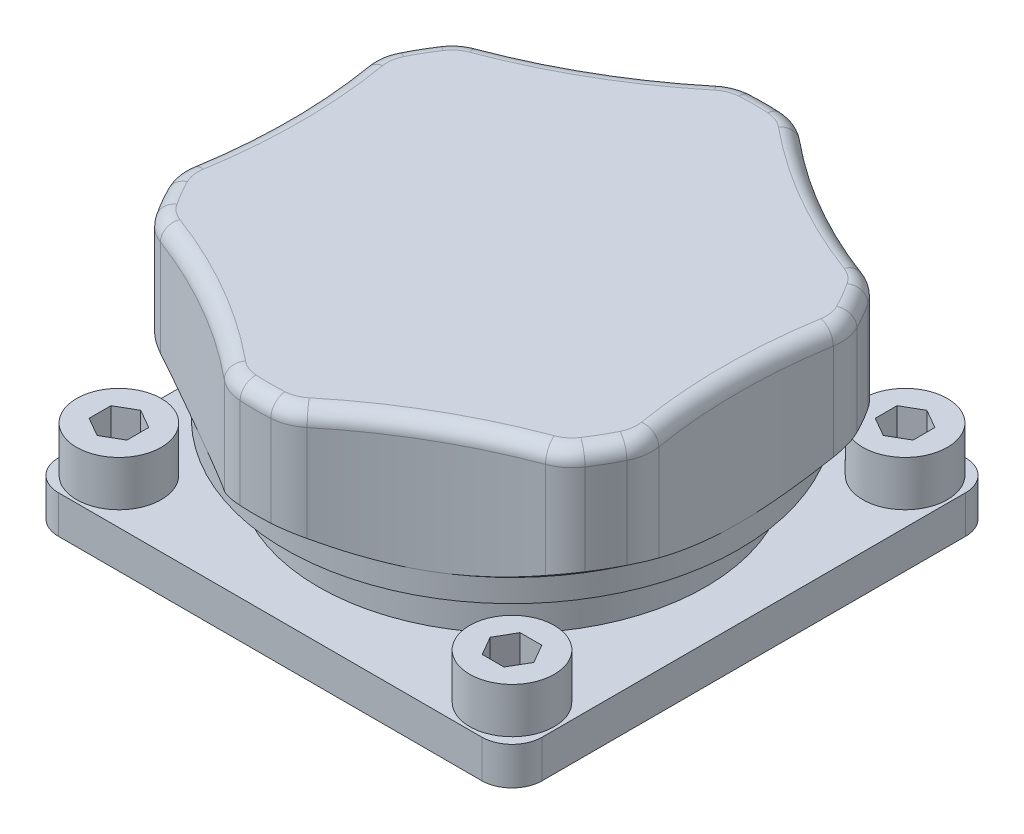
SolidWorks part; units mm, degrees
ref_plane "前视基准面" through (0, 0, 0) normal (0, 0, 1) x (1, 0, 0)
ref_plane "上视基准面" through (0, 0, 0) normal (0, 1, 0) x (1, 0, 0)
ref_plane "右视基准面" through (0, 0, 0) normal (1, 0, 0) x (0, 0, -1)
sketch "草图1" plane through (0, 0, 0) normal (0, 1, 0) x (1, 0, 0)
  line L1 (14, -16) -> (-14, -16)
  line L2 (16, -14) -> (16, 14)
  line L3 (14, 16) -> (-14, 16)
  line L4 (-16, -14) -> (-16, 14)
  line L5 (16, -16) -> (-16, 16) construction
  line L6 (16, 16) -> (-16, -16) construction
  arc A0 (-14, -16) -> (-16, -14) centre (-14, -14) cw
  arc A1 (14, -16) -> (16, -14) centre (14, -14) ccw
  arc A2 (16, 14) -> (14, 16) centre (14, 14) ccw
  arc A3 (-14, 16) -> (-16, 14) centre (-14, 14) ccw
  point P0 (0, 0)
  dimension "D3" = 2
  dimension "D1" = 32
  dimension "D2" = 32
extrude "凸台-拉伸1" add sketch "草图1" along normal blind 2.5
sketch "草图2" plane through (0, 2.5, 0) normal (0, 1, 0) x (1, 0, 0)
  circle A0 centre (0, 0) radius 12.8
  dimension "D1" = 25.6
extrude "凸台-拉伸2" add sketch "草图2" along normal blind 10
sketch "草图3" plane through (0, 2.5, 0) normal (0, 1, 0) x (1, 0, 0)
  circle A0 centre (0, 0) radius 17
  dimension "D1" = 34
extrude "凸台-拉伸3" add sketch "草图3" along normal blind 10 from offset 3.25
sketch "草图4" plane through (0, 0, 0) normal (0, 0, 1) x (1, 0, 0)
  line L0 (-17, 5.75) -> (-15, 5.75)
  line L1 (-17, 5.75) -> (17, 5.75) construction
  line L2 (-15, 5.75) -> (-15, 7.25)
  line L3 (-15, 7.25) -> (-17, 8.75)
  line L4 (-17, 15.75) -> (-17, 5.75) construction
  line L5 (-17, 8.75) -> (-17, 5.75)
  line L6 (0, 0) -> (0, 15.75) construction
  line L7 (-14, 0) -> (14, 0) construction
  line L8 (17, 15.75) -> (-17, 15.75) construction
  dimension "D1" = 1.5
  dimension "D2" = 15
  dimension "D3" = 3
revolve "切除-旋转1" cut sketch "草图4" angle 360 about L6
sketch "草图5" plane through (0, 15.75, 0) normal (0, 1, 0) x (1, 0, 0)
  line L0 (0, 0) -> (50, 0) construction
  circle A0 centre (50, 0) radius 35
  circle A1 centre (25, -43.3013) radius 35
  circle A2 centre (-25, -43.3013) radius 35
  circle A3 centre (-50, 0) radius 35
  circle A4 centre (-25, 43.3013) radius 35
  circle A5 centre (25, 43.3013) radius 35
  circle M2 centre (0, 0) radius 17
  dimension "D3" = 70
  dimension "D2" = 50
  dimension "D1" = 6
extrude "切除-拉伸2" cut sketch "草图5" against normal blind 10 contours A5 M2 | A0 A5 A4 M2 | A3 | A2 | A1
sketch "草图7" plane through (0, 2.5, 0) normal (0, 1, 0) x (1, 0, 0)
  line L0 (-15.4142, -15.4142) -> (0, 0) construction
  line L1 (0, 0) -> (-13, -13) construction
  arc A0 (-16, -14) -> (-14, -16) centre (-14, -14) ccw construction
  circle A1 centre (-13, -13) radius 2.8
  circle A2 centre (-13, 13) radius 2.8
  circle A3 centre (13, 13) radius 2.8
  circle A4 centre (13, -13) radius 2.8
  dimension "D1" = 5.6
  dimension "D2" = 13
  dimension "D4" = 18.3848
  dimension "D3" = 4
extrude "凸台-拉伸4" add sketch "草图7" along normal blind 3
sketch "草图8" plane through (0, 5.5, 0) normal (0, 1, 0) x (1, 0, 0)
  line L0 (13, 13) -> (13, 14.4434) construction
  line L1 (13, 14.4434) -> (11.75, 13.7217)
  line L2 (11.75, 13.7217) -> (11.75, 12.2783)
  line L3 (11.75, 12.2783) -> (13, 11.5566)
  line L4 (13, 11.5566) -> (14.25, 12.2783)
  line L5 (14.25, 12.2783) -> (14.25, 13.7217)
  line L6 (14.25, 13.7217) -> (13, 14.4434)
  circle A0 centre (13, 13) radius 1.25 construction
  dimension "D1" = 2.5
extrude "切除-拉伸4" cut sketch "草图8" against normal blind 2
pattern_circular "阵列(圆周)1" count 4 over 360 about axis through (0, 0, 0) along (0, 1, 0) of "切除-拉伸4"
fillet "圆角1" radius 3 12 edges at (-15.64, 12.25, 6.6626) (-15.64, 12.25, -6.6626) (-2.05, 12.25, 16.8759) (-13.59, 12.25, 10.2133) (13.59, 12.25, 10.2133) (2.05, 12.25, 16.8759) (15.64, 12.25, -6.6626) (15.64, 12.25, 6.6626) (-13.59, 12.25, -10.2133) (-2.05, 12.25, -16.8759) (2.05, 12.25, -16.8759) (13.59, 12.25, -10.2133)
fillet "圆角2" radius 1 24 edges at (-13.5551, 15.75, -10.0565) (-7.5, 15.75, -12.9904) (-1.9316, 15.75, -16.7673) (0, 15.75, -17) (1.9316, 15.75, -16.7673) (7.5, 15.75, -12.9904) (13.5551, 15.75, -10.0565) (14.7224, 15.75, -8.5) (15.4867, 15.75, -6.7108) (15, 15.75, 0) (15.4867, 15.75, 6.7108) (14.7224, 15.75, 8.5) (13.5551, 15.75, 10.0565) (7.5, 15.75, 12.9904) (1.9316, 15.75, 16.7673) (0, 15.75, 17) (-1.9316, 15.75, 16.7673) (-7.5, 15.75, 12.9904) (-13.5551, 15.75, 10.0565) (-14.7224, 15.75, 8.5) (-15.4867, 15.75, 6.7108) (-15, 15.75, 0) (-15.4867, 15.75, -6.7108) (-14.7224, 15.75, -8.5)
